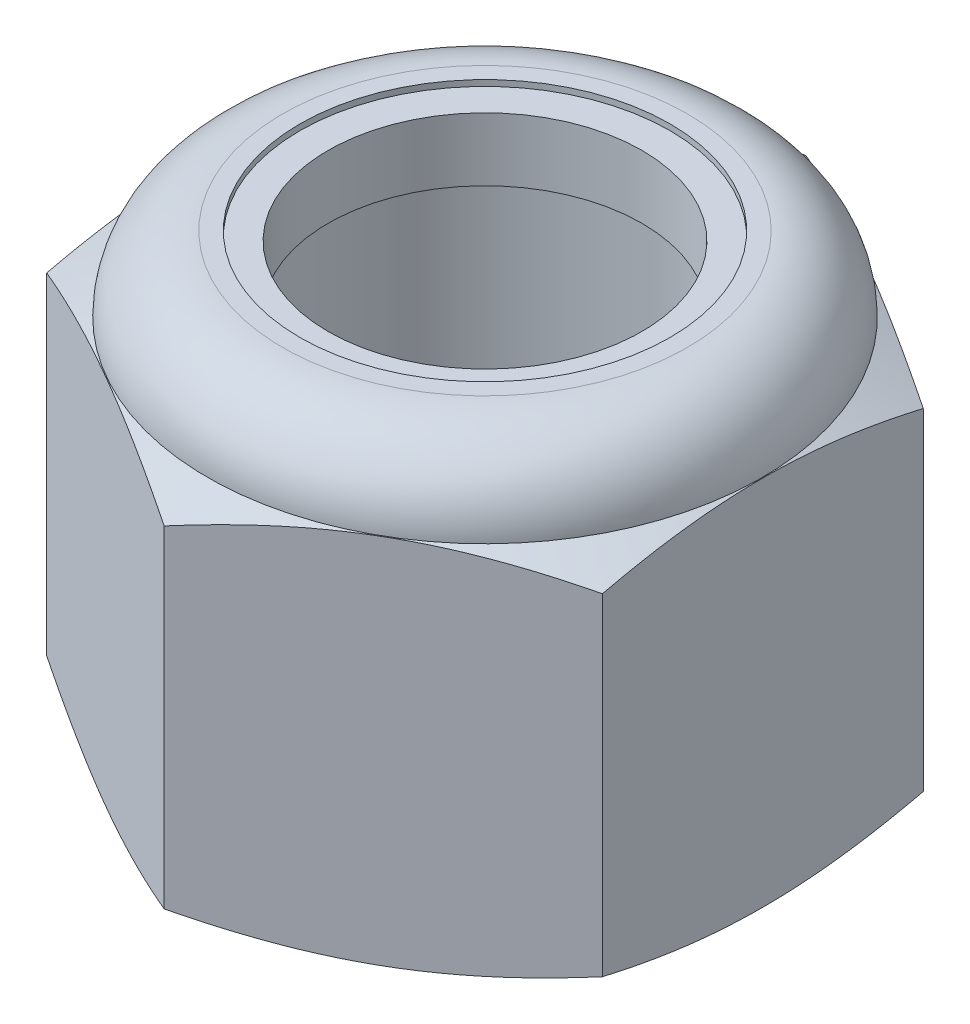
SolidWorks part; units mm, degrees
material "Alloy Steel"
ref_plane "Front Plane" through (0, 0, 0) normal (0, 0, 1) x (1, 0, 0)
ref_plane "Top Plane" through (0, 0, 0) normal (0, 1, 0) x (1, 0, 0)
ref_plane "Right Plane" through (0, 0, 0) normal (1, 0, 0) x (0, 0, -1)
sketch "Sketch1" plane through (0, 0, 0) normal (0, 1, 0) x (1, 0, 0)
  line L0 (0, 0) -> (0, 8.2562) construction
  line L2 (0, 8.2562) -> (-7.1501, 4.1281)
  line L3 (-7.1501, 4.1281) -> (-7.1501, -4.1281)
  line L4 (-7.1501, -4.1281) -> (0, -8.2562)
  line L5 (0, -8.2562) -> (7.1501, -4.1281)
  line L6 (7.1501, -4.1281) -> (7.1501, 4.1281)
  line L7 (7.1501, 4.1281) -> (0, 8.2562)
  circle A0 centre (0, 0) radius 7.1501 construction
  dimension "D1" = 14.3002
extrude "Boss-Extrude1" add sketch "Sketch1" along normal blind 11.5094
sketch "Sketch2" plane through (0, 11.5094, 0) normal (0, 1, 0) x (1, 0, 0)
  circle A0 centre (0, 0) radius 4.7625
  dimension "D1" = 9.525
extrude "Cut-Extrude1" cut sketch "Sketch2" against normal through all
sketch "Sketch4" plane through (0, 0, 0) normal (1, 0, 0) x (0, 0, -1)
  line L0 (0, 0) -> (7.1386, 0)
  line L2 (8.2562, 11.5094) -> (8.2562, 0) construction
  line L3 (8.2562, 0.5211) -> (8.2562, 9.0578)
  line L4 (8.2562, 9.0578) -> (7.1386, 9.579)
  line L5 (4.1281, 11.5094) -> (8.2562, 11.5094) construction
  line L6 (5.2082, 11.5094) -> (5.2082, 12.7794)
  line L7 (5.2082, 12.7794) -> (9.5262, 12.7794)
  line L8 (9.5262, 12.7794) -> (9.5262, -1.27)
  line L9 (9.5262, -1.27) -> (0, -1.27)
  line L10 (0, -1.27) -> (0, 0)
  line L11 (-4.1281, 0) -> (4.1281, 0) construction
  line L12 (4.1281, 0) -> (8.2562, 0) construction
  line L13 (7.1386, 0) -> (8.2562, 0.5211)
  line L14 (7.1386, 0) -> (7.1386, 9.579) construction
  line L15 (0, 0) -> (0, 9.6306) construction
  arc A0 (7.1386, 9.579) -> (5.2082, 11.5094) centre (5.2082, 9.579) ccw
  dimension "D1" = 1.27
  dimension "D2" = 25
  dimension "D3" = 1.9304
  dimension "D4" = 1.1176
  dimension "D5" = 1.27
revolve "Cut-Revolve1" cut sketch "Sketch4" angle 360 about L15
sketch "Sketch5" plane through (0, 0, 0) normal (1, 0, 0) x (0, 0, -1)
  line L0 (6.9862, 9.579) -> (0, 9.579)
  line L1 (7.1386, 9.579) -> (-7.1386, 9.579) construction
  line L2 (0, 9.579) -> (0, 12.119)
  line L3 (0, 12.119) -> (4.6228, 12.119)
  line L4 (4.6228, 12.119) -> (4.6228, 11.357)
  line L5 (4.6228, 11.357) -> (5.2082, 11.357)
  line L6 (5.2082, 11.357) -> (5.2082, 11.5094) construction
  line L7 (5.2082, 11.5094) -> (-5.2082, 11.5094) construction
  arc A0 (5.2082, 11.357) -> (6.9862, 9.579) centre (5.2082, 9.579) cw
  arc A1 (7.1386, 9.579) -> (5.2082, 11.5094) centre (5.2082, 9.579) ccw construction
  dimension "D1" = 0.1524
  dimension "D2" = 4.6228
  dimension "D3" = 2.54
revolve "Cut-Revolve2" cut sketch "Sketch5" angle 360 about L2
sketch "Sketch6" plane through (0, 0, 0) normal (1, 0, 0) x (0, 0, -1)
  line L1 (4.0386, 9.6552) -> (4.0386, 11.2808)
  line L2 (4.0386, 11.2808) -> (5.2082, 11.2808)
  line L3 (4.7625, 11.5094) -> (-4.7625, 11.5094) construction
  line L5 (-5.2082, 11.357) -> (5.2082, 11.357) construction
  line L6 (6.9083, 9.6552) -> (4.0386, 9.6552)
  line L7 (7.1386, 9.579) -> (-7.1386, 9.579) construction
  line L8 (0, 0) -> (0, 11.5094) construction
  arc A0 (6.9083, 9.6552) -> (5.2082, 11.2808) centre (5.2082, 9.579) ccw
  arc A4 (6.9862, 9.579) -> (5.2082, 11.357) centre (5.2082, 9.579) ccw construction
  dimension "D1" = 0.0762
  dimension "D2" = 0.0762
  dimension "D3" = 4.0386
revolve "Revolve1" add sketch "Sketch6" angle 360 about L8
